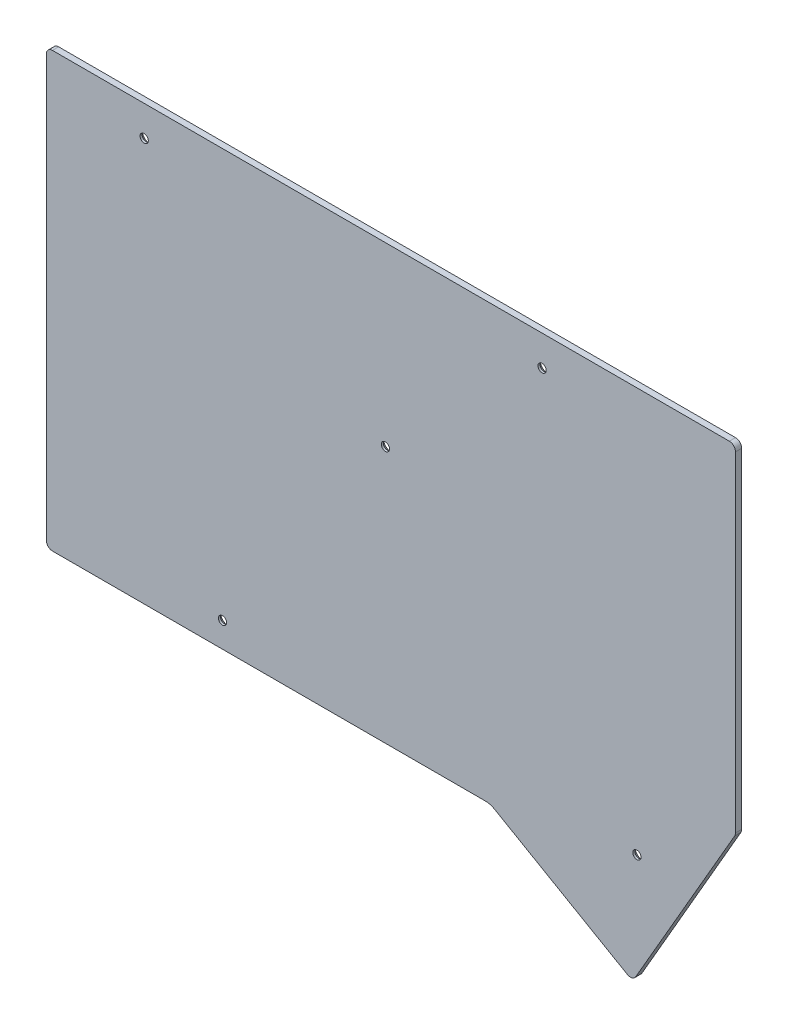
SolidWorks part; units mm, degrees
ref_plane "Front Plane" through (0, 0, 0) normal (0, 0, 1) x (1, 0, 0)
ref_plane "Top Plane" through (0, 0, 0) normal (0, 1, 0) x (1, 0, 0)
ref_plane "Right Plane" through (0, 0, 0) normal (1, 0, 0) x (0, 0, -1)
sketch "Sketch1" plane through (0, 0, 0) normal (0, 0, 1) x (1, 0, 0)
  line L6 (20.7161, 151.9249) -> (-143.4339, 151.9249)
  line L7 (-144.9339, 150.4249) -> (-144.9339, 48.2618)
  line L8 (-143.4339, 46.7618) -> (-38.4936, 46.7618)
  line L9 (-36.2436, 46.1589) -> (-4.0178, 27.5534)
  line L10 (-1.9688, 28.1024) -> (22.0152, 69.6439)
  line L11 (22.2161, 70.3939) -> (22.2161, 150.4249)
  line L12 (20.7161, 151.9249) -> (-143.4339, 151.9249)
  line L13 (-144.9339, 150.4249) -> (-144.9339, 48.2618)
  line L14 (-143.4339, 46.7618) -> (-38.4936, 46.7618)
  line L15 (-36.2436, 46.1589) -> (-4.0178, 27.5534)
  line L16 (-1.9688, 28.1024) -> (22.0152, 69.6439)
  line L17 (22.2161, 70.3939) -> (22.2161, 150.4249)
  circle A0 centre (-24.6966, 144.5751) radius 1 construction
  circle A1 centre (-24.6966, 144.5751) radius 1
  circle A2 centre (-121.1966, 144.5751) radius 1 construction
  circle A3 centre (-121.1966, 144.5751) radius 1
  circle A4 centre (-62.6966, 109.0751) radius 1 construction
  circle A5 centre (-62.6966, 109.0751) radius 1
  arc A6 (22.2161, 150.4249) -> (20.7161, 151.9249) centre (20.7161, 150.4249) ccw
  arc A7 (-143.4339, 151.9249) -> (-144.9339, 150.4249) centre (-143.4339, 150.4249) ccw
  arc A8 (-144.9339, 48.2618) -> (-143.4339, 46.7618) centre (-143.4339, 48.2618) ccw
  arc A9 (-36.2436, 46.1589) -> (-38.4936, 46.7618) centre (-38.4936, 42.2618) ccw
  arc A10 (-4.0178, 27.5534) -> (-1.9688, 28.1024) centre (-3.2678, 28.8524) ccw
  arc A11 (22.0152, 69.6439) -> (22.2161, 70.3939) centre (20.7161, 70.3939) ccw
  arc A12 (22.2161, 150.4249) -> (20.7161, 151.9249) centre (20.7161, 150.4249) ccw
  arc A13 (-143.4339, 151.9249) -> (-144.9339, 150.4249) centre (-143.4339, 150.4249) ccw
  arc A14 (-144.9339, 48.2618) -> (-143.4339, 46.7618) centre (-143.4339, 48.2618) ccw
  arc A15 (-36.2436, 46.1589) -> (-38.4936, 46.7618) centre (-38.4936, 42.2618) ccw
  arc A16 (-4.0178, 27.5534) -> (-1.9688, 28.1024) centre (-3.2678, 28.8524) ccw
  arc A17 (22.0152, 69.6439) -> (22.2161, 70.3939) centre (20.7161, 70.3939) ccw
  circle A18 centre (-102.1966, 52.8251) radius 1 construction
  circle A19 centre (-102.1966, 52.8251) radius 1
  circle A20 centre (-1.6966, 53.825) radius 1 construction
  circle A21 centre (-1.6966, 53.825) radius 1
  dimension "D1" = 0
extrude "Boss-Extrude1" add sketch "Sketch1" along normal blind 1.5
chamfer "Chamfer1" distance 1 angle 45 5 edges at (-23.6966, 144.5751, 0) (-120.1966, 144.5751, 0) (-61.6966, 109.0751, 0) (-0.6966, 53.825, 0) (-101.1966, 52.8251, 0)
